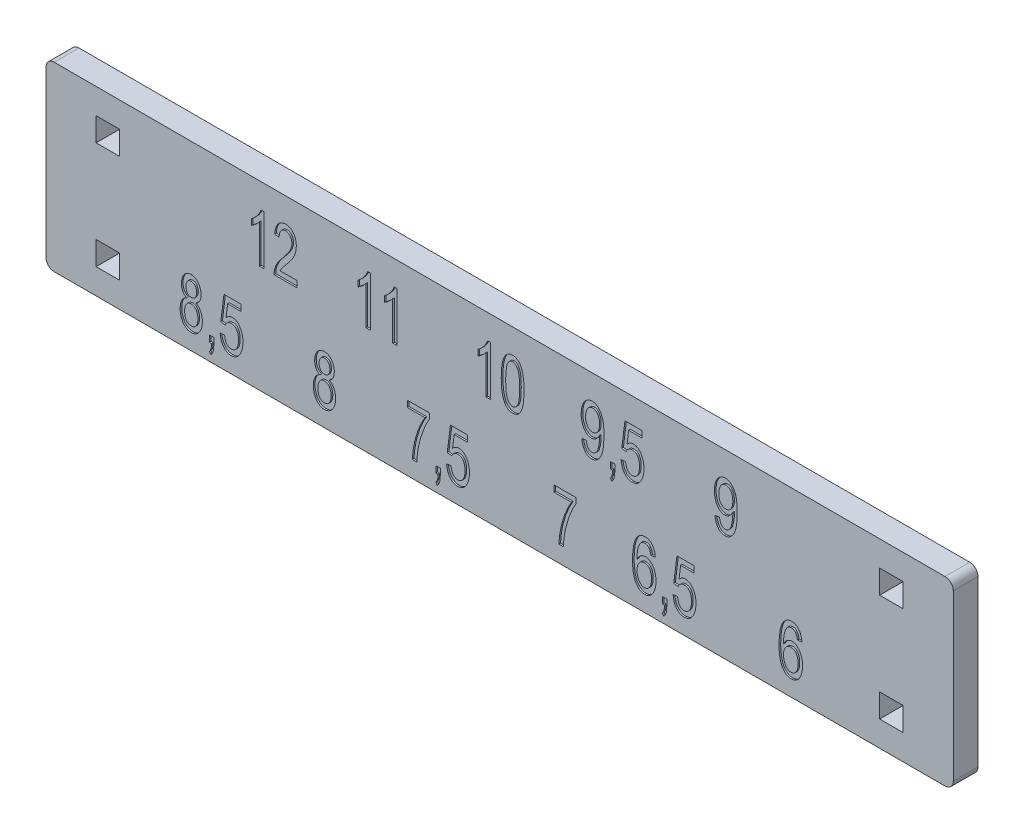
SolidWorks part; units mm, degrees
ref_plane "Спереди" through (0, 0, 0) normal (0, 0, 1) x (1, 0, 0)
ref_plane "Сверху" through (0, 0, 0) normal (0, 1, 0) x (1, 0, 0)
ref_plane "Справа" through (0, 0, 0) normal (1, 0, 0) x (0, 0, -1)
sketch "Эскиз2" plane through (0, 0, 0) normal (0, 0, 1) x (1, 0, 0)
  line L0 (-15.9107, 0) -> (16.719, 0) construction
  line L1 (-55, 11) -> (55, 11)
  line L2 (-55, 11) -> (-55, -11)
  line L3 (-55, -11) -> (55, -11)
  line L4 (55, 11) -> (55, -11)
  line L5 (-55, 11) -> (55, -11) construction
  line L6 (-55, -11) -> (55, 11) construction
  line L11 (-48.925, -5.075) -> (-46.075, -7.925) construction
  line L12 (-48.925, -7.925) -> (-46.075, -5.075) construction
  line L13 (-46.075, -7.925) -> (-46.075, -5.075)
  line L14 (-48.925, -5.075) -> (-46.075, -5.075)
  line L19 (-35.25, -19.9206) -> (35.25, -19.9206) construction
  line L20 (-48.925, -7.925) -> (-48.925, -5.075)
  line L21 (-48.925, 7.925) -> (-46.075, 7.925)
  line L22 (-48.925, 7.925) -> (-48.925, 5.075)
  line L23 (-48.925, 5.075) -> (-46.075, 5.075)
  line L24 (-46.075, 7.925) -> (-46.075, 5.075)
  line L25 (-48.925, 7.925) -> (-46.075, 5.075) construction
  line L26 (-48.925, 5.075) -> (-46.075, 7.925) construction
  line L27 (-48.925, -7.925) -> (-46.075, -7.925)
  line L28 (0, 0) -> (0, 20.7293) construction
  line L29 (46.075, -7.925) -> (46.075, -5.075)
  line L30 (48.925, -7.925) -> (46.075, -5.075) construction
  line L31 (48.925, -5.075) -> (46.075, -7.925) construction
  line L32 (48.925, -7.925) -> (46.075, -7.925)
  line L33 (48.925, -7.925) -> (48.925, -5.075)
  line L34 (48.925, -5.075) -> (46.075, -5.075)
  line L35 (48.925, 5.075) -> (46.075, 7.925) construction
  line L36 (48.925, 7.925) -> (46.075, 5.075) construction
  line L37 (46.075, 7.925) -> (46.075, 5.075)
  line L38 (48.925, 5.075) -> (46.075, 5.075)
  line L39 (48.925, 7.925) -> (48.925, 5.075)
  line L40 (48.925, 7.925) -> (46.075, 7.925)
  point P0 (0, 0)
  point P14 (-47.5, -6.5)
  point P20 (0, -19.9206)
  point P21 (-47.5, 6.5)
  point P31 (47.5, 6.5)
  dimension "D1" = 22
  dimension "D2" = 4.5
  dimension "D3" = 7.5
  dimension "D4" = 110
  dimension "D6" = 70.5
  dimension "D7" = 2.85
extrude "Бобышка-Вытянуть1" add sketch "Эскиз2" along normal blind 3
fillet "Скругление1" radius 1 4 edges at (-55, -11, 1.5) (-55, 11, 1.5) (55, -11, 1.5) (55, 11, 1.5)
sketch "Эскиз3" [suppressed] plane through (0, 0, 3) normal (0, 0, 1) x (1, 0, 0)
  line L0 (-31, 0.6827) -> (-17, 0.6827) construction
  line L1 (-17, 0.6827) -> (-3, 0.6827) construction
  line L2 (-3, 0.6827) -> (11, 0.6827) construction
  line L3 (11, 0.6827) -> (25, 0.6827) construction
  line L4 (-3, 0.6827) -> (0, 0.6827) construction
  line L5 (-38.25, -4.6945) -> (-24.15, -4.6945) construction
  line L6 (-24.15, -4.6945) -> (-10.05, -4.6945) construction
  line L7 (-10.05, -4.6945) -> (4.05, -4.6945) construction
  line L8 (4.05, -4.6945) -> (18.15, -4.6945) construction
  line L9 (18.15, -4.6945) -> (32.25, -4.6945) construction
  line L10 (-3, -4.6945) -> (0, -4.6945) construction
  text T0 "12\r\n"
  text T1 "11\r\n"
  text T2 "10\r\n"
  text T3 "9,5\r\n"
  text T4 "9\r\n"
  text T5 "8,5\r\n"
  text T6 "8\r\n"
  text T7 "7,5\r\n"
  text T8 "7\r\n\r\n"
  text T9 "6,5\r\n"
  text T10 "6\r\n"
  dimension "D1" = 56
  dimension "D2" = 3
  dimension "D3" = 70.5
  dimension "D4" = 3
sketch "Эскиз4" plane through (0, 0, 3) normal (0, 0, 1) x (1, 0, 0)
  line L0 (28, 2.0237) -> (14, 2.0237) construction
  line L1 (14, 2.0237) -> (0, 2.0237) construction
  line L2 (0, 2.0237) -> (-14, 2.0237) construction
  line L3 (-14, 2.0237) -> (-28, 2.0237) construction
  line L4 (-35.5, -9) -> (-21.3, -9) construction
  line L5 (-21.3, -9) -> (-7.1, -9) construction
  line L6 (-7.1, -9) -> (7.1, -9) construction
  line L7 (7.1, -9) -> (21.3, -9) construction
  line L8 (21.3, -9) -> (35.5, -9) construction
  line L9 (-35.5, -9) -> (-38.9658, -9) construction
  line L10 (-28, 2.0237) -> (-32.3442, 2.0237) construction
  line L11 (28, 2.0237) -> (31.7847, 2.0237) construction
  line L12 (-54, -11) -> (54, -11) construction
  text T0 " 12    11     10    9,5     9" font "Arial" height 6
  text T1 "8,5     8     7,5      7    6,5      6" font "Arial" height 6
  point P12 (0, -9)
  dimension "D1" = 56
  dimension "D2" = 71
  dimension "D3" = 2
extrude "Вырез-Вытянуть1" cut sketch "Эскиз4" against normal blind 0.2
